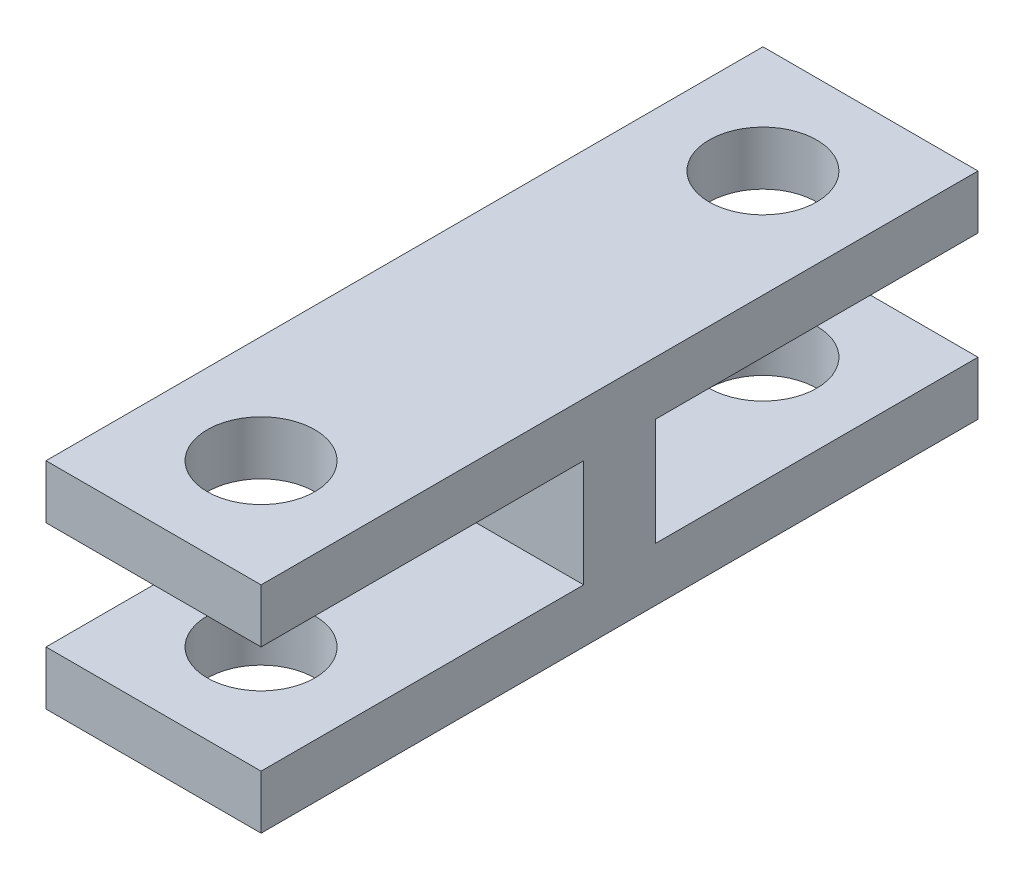
SolidWorks part; units mm, degrees
ref_plane "Front Plane" through (0, 0, 0) normal (0, 0, 1) x (1, 0, 0)
ref_plane "Top Plane" through (0, 0, 0) normal (0, 1, 0) x (1, 0, 0)
ref_plane "Right Plane" through (0, 0, 0) normal (1, 0, 0) x (0, 0, -1)
sketch "Sketch1" plane through (0, 0, 0) normal (1, 0, 0) x (0, 0, -1)
  line L0 (-4.5819, -8.6082) -> (4.4181, -8.6082)
  line L1 (4.4181, -8.6082) -> (4.4181, -5.6082)
  line L2 (4.4181, -5.6082) -> (-4.5819, -5.6082)
  line L3 (-4.5819, -5.6082) -> (-4.5819, -4.1082)
  line L4 (-4.5819, -4.1082) -> (15.4181, -4.1082)
  line L5 (15.4181, -4.1082) -> (15.4181, -5.6082)
  line L6 (15.4181, -5.6082) -> (6.4181, -5.6082)
  line L7 (6.4181, -5.6082) -> (6.4181, -8.6082)
  line L8 (6.4181, -8.6082) -> (15.4181, -8.6082)
  line L9 (15.4181, -8.6082) -> (15.4181, -10.1082)
  line L10 (15.4181, -10.1082) -> (-4.5819, -10.1082)
  line L11 (-4.5819, -10.1082) -> (-4.5819, -8.6082)
  point P11 (10.9181, -5.6082)
  dimension "D1" = 1.5
  dimension "D2" = 3
  dimension "D3" = 9
  dimension "D4" = 20
extrude "Boss-Extrude1" add sketch "Sketch1" along normal blind 6
sketch "Sketch2" plane through (0, -4.1082, 0) normal (0, 1, 0) x (1, 0, 0)
  line L0 (0, -1.5819) -> (6, -1.5819) construction
  line L1 (0, 15.4181) -> (0, -4.5819) construction
  line L2 (6, 15.4181) -> (6, -4.5819) construction
  line L3 (0, 12.4181) -> (6, 12.4181) construction
  line L4 (6, -4.5819) -> (0, -4.5819) construction
  line L5 (6, 15.4181) -> (0, 15.4181) construction
  circle A0 centre (3, -1.5819) radius 1.5
  circle A1 centre (3, 12.4181) radius 1.5
  dimension "D1" = 3
  dimension "D2" = 3
  dimension "D3" = 3
extrude "Cut-Extrude1" cut sketch "Sketch2" against normal through all
